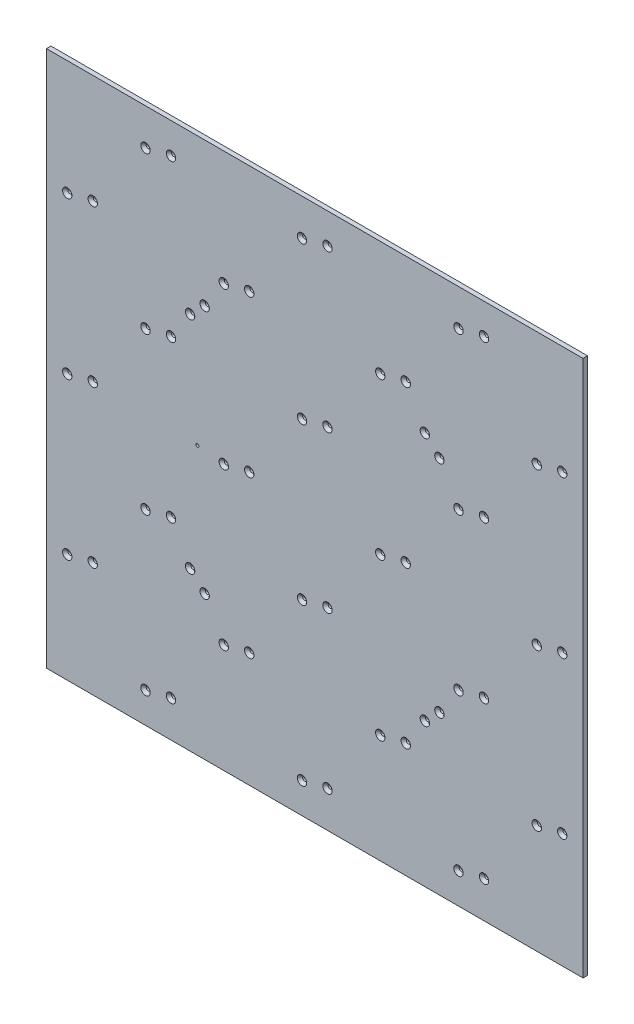
SolidWorks part; units mm, degrees
material "6063-T1"
ref_plane "Front Plane" through (0, 0, 0) normal (0, 0, 1) x (1, 0, 0)
ref_plane "Top Plane" through (0, 0, 0) normal (0, 1, 0) x (1, 0, 0)
ref_plane "Right Plane" through (0, 0, 0) normal (1, 0, 0) x (0, 0, -1)
sketch "Sketch1" plane through (0, 0, 0) normal (0, 0, 1) x (1, 0, 0)
  line L1 (600, -600) -> (-600, -600)
  line L2 (600, -600) -> (600, 600)
  line L3 (600, 600) -> (-600, 600)
  line L4 (-600, -600) -> (-600, 600)
  line L5 (600, -600) -> (-600, 600) construction
  line L6 (600, 600) -> (-600, -600) construction
  point P0 (0, 0)
  dimension "D1" = 1200
  dimension "D2" = 1200
extrude "Boss-Extrude1" add sketch "Sketch1" against normal blind 10 from offset 3
sketch "Sketch2" plane through (0, 0, -7) normal (0, 0, -1) x (-1, 0, 0)
  circle A0 centre (246.2365, -278.7635) radius 4.5
  circle A1 centre (278.7635, -246.2365) radius 4.5
  circle A2 centre (-246.2365, -278.7635) radius 4.5
  circle A3 centre (-278.7635, -246.2365) radius 4.5
  circle A4 centre (-278.7635, 246.2365) radius 4.5
  circle A5 centre (-246.2365, 278.7635) radius 4.5
  circle A6 centre (278.7635, 246.2365) radius 4.5
  circle A7 centre (246.2365, 278.7635) radius 4.5
  circle A8 centre (378.5001, -531.5724) radius 4.5
  circle A9 centre (321.5073, -518.4202) radius 4.5
  circle A10 centre (553.502, -356.5705) radius 4.5
  circle A11 centre (496.5092, -343.4183) radius 4.5
  circle A12 centre (28.4964, -531.5724) radius 4.5
  circle A13 centre (-28.4964, -518.4202) radius 4.5
  circle A14 centre (203.4983, -356.5705) radius 4.5
  circle A15 centre (146.5055, -343.4183) radius 4.5
  circle A16 centre (378.5001, -181.5687) radius 4.5
  circle A17 centre (321.5073, -168.4165) radius 4.5
  circle A18 centre (553.502, -6.5668) radius 4.5
  circle A19 centre (496.5092, 6.5854) radius 4.5
  circle A20 centre (553.502, 343.4369) radius 4.5
  circle A21 centre (496.5092, 356.5891) radius 4.5
  circle A22 centre (378.5001, 518.4388) radius 4.5
  circle A23 centre (321.5073, 531.591) radius 4.5
  circle A24 centre (378.5001, 168.4351) radius 4.5
  circle A25 centre (321.5073, 181.5872) radius 4.5
  circle A26 centre (203.4983, 343.4369) radius 4.5
  circle A27 centre (146.5055, 356.5891) radius 4.5
  circle A28 centre (203.4983, -6.5668) radius 4.5
  circle A29 centre (146.5055, 6.5854) radius 4.5
  circle A30 centre (28.4964, 168.4351) radius 4.5
  circle A31 centre (-28.4964, 181.5872) radius 4.5
  circle A32 centre (28.4964, -181.5687) radius 4.5
  circle A33 centre (-28.4964, -168.4165) radius 4.5
  circle A34 centre (-146.5055, -6.5668) radius 4.5
  circle A35 centre (-203.4983, 6.5854) radius 4.5
  circle A36 centre (-146.5055, -356.5705) radius 4.5
  circle A37 centre (-203.4983, -343.4183) radius 4.5
  circle A38 centre (-321.5073, -181.5687) radius 4.5
  circle A39 centre (-378.5001, -168.4165) radius 4.5
  circle A40 centre (-553.502, -343.4183) radius 4.5
  circle A41 centre (-496.5092, -356.5705) radius 4.5
  circle A42 centre (-378.5001, -518.4202) radius 4.5
  circle A43 centre (-321.5073, -531.5724) radius 4.5
  circle A44 centre (28.4964, 518.4388) radius 4.5
  circle A45 centre (-28.4964, 531.591) radius 4.5
  circle A46 centre (-321.5073, 518.4388) radius 4.5
  circle A47 centre (-378.5001, 531.591) radius 4.5
  circle A48 centre (-146.5055, 343.4369) radius 4.5
  circle A49 centre (-203.4983, 356.5891) radius 4.5
  circle A50 centre (-496.5092, 343.4369) radius 4.5
  circle A51 centre (-553.502, 356.5891) radius 4.5
  circle A52 centre (-321.5073, 168.4351) radius 4.5
  circle A53 centre (-378.5001, 181.5872) radius 4.5
  circle A54 centre (-496.5092, -6.5668) radius 4.5
  circle A55 centre (-553.502, 6.5854) radius 4.5
  dimension "D1" = 9
extrude "Cut-Extrude1" cut sketch "Sketch2" against normal through all
chamfer "Chamfer1" distance 6 angle 45 56 edges at (-250.7365, -278.7635, 3) (-283.2635, -246.2365, 3) (241.7365, -278.7635, 3) (274.2635, -246.2365, 3) (274.2635, 246.2365, 3) (241.7365, 278.7635, 3) (-283.2635, 246.2365, 3) (-250.7365, 278.7635, 3) (-383.0001, -531.5724, 3) (-326.0073, -518.4202, 3) (-558.002, -356.5705, 3) (-501.0092, -343.4183, 3) (-32.9964, -531.5724, 3) (23.9964, -518.4202, 3) (-207.9983, -356.5705, 3) (-151.0055, -343.4183, 3) (-383.0001, -181.5687, 3) (-326.0073, -168.4165, 3) (-558.002, -6.5668, 3) (-501.0092, 6.5854, 3) (-558.002, 343.4369, 3) (-501.0092, 356.5891, 3) (-383.0001, 518.4388, 3) (-326.0073, 531.591, 3) (-383.0001, 168.4351, 3) (-326.0073, 181.5872, 3) (-207.9983, 343.4369, 3) (-151.0055, 356.5891, 3) (-207.9983, -6.5668, 3) (-151.0055, 6.5854, 3) (-32.9964, 168.4351, 3) (23.9964, 181.5872, 3) (-32.9964, -181.5687, 3) (23.9964, -168.4165, 3) (142.0055, -6.5668, 3) (198.9983, 6.5854, 3) (142.0055, -356.5705, 3) (198.9983, -343.4183, 3) (317.0073, -181.5687, 3) (374.0001, -168.4165, 3) (549.002, -343.4183, 3) (492.0092, -356.5705, 3) (374.0001, -518.4202, 3) (317.0073, -531.5724, 3) (-32.9964, 518.4388, 3) (23.9964, 531.591, 3) (317.0073, 518.4388, 3) (374.0001, 531.591, 3) (142.0055, 343.4369, 3) (198.9983, 356.5891, 3) (492.0092, 343.4369, 3) (549.002, 356.5891, 3) (317.0073, 168.4351, 3) (374.0001, 181.5872, 3) (492.0092, -6.5668, 3) (549.002, 6.5854, 3)
sketch "Sketch3" plane through (0, 0, 3) normal (0, 0, 1) x (1, 0, 0)
  circle A0 centre (-262.5, 0) radius 3.4
  dimension "D1" = 6.8
extrude "Cut-Extrude2" cut sketch "Sketch3" against normal up to next
sketch "Sketch6" plane through (0, 0, 3) normal (0, 0, 1) x (1, 0, 0)
  line L0 (-350, 525) -> (-350, -525) construction
  line L1 (-525, 525) -> (525, 525) construction
  line L2 (-525, 525) -> (-525, -525) construction
  line L3 (-525, -525) -> (525, -525) construction
  line L4 (525, 525) -> (525, -525) construction
  line L5 (-525, 525) -> (525, -525) construction
  line L6 (-525, -525) -> (525, 525) construction
  line L7 (-175, 525) -> (-175, -525) construction
  line L8 (0, 525) -> (0, -525) construction
  line L9 (175, 525) -> (175, -525) construction
  line L10 (350, 525) -> (350, -525) construction
  line L11 (-525, 350) -> (525, 350) construction
  line L12 (-525, 175) -> (525, 175) construction
  line L13 (-525, 0) -> (525, 0) construction
  line L14 (-525, -175) -> (525, -175) construction
  line L15 (-525, -350) -> (525, -350) construction
  line L16 (175, 350) -> (350, 175) construction
  line L17 (535.6066, 45.9619) -> (570.9619, 10.6066) construction
  line L18 (535.6066, 45.9619) -> (479.0381, -10.6066) construction
  line L19 (479.0381, -10.6066) -> (514.3934, -45.9619) construction
  line L20 (570.9619, 10.6066) -> (514.3934, -45.9619) construction
  line L21 (535.6066, 45.9619) -> (514.3934, -45.9619) construction
  line L22 (479.0381, -10.6066) -> (570.9619, 10.6066) construction
  line L23 (350, -175) -> (175, -350) construction
  line L24 (-175, -350) -> (-350, -175) construction
  line L25 (-350, 175) -> (-175, 350) construction
  circle A1 centre (496.5092, -6.5668) radius 4.5
  circle A2 centre (496.5092, -6.5668) radius 4.5
  circle A3 centre (553.502, 6.5854) radius 4.5
  circle A4 centre (553.502, 6.5854) radius 4.5
  point P0 (0, 0)
  point P47 (0, 0)
  dimension "D1" = 1050
  dimension "D3" = 175
  dimension "D5" = 175
  dimension "D6" = 80
  dimension "D7" = 50
  dimension "D8" = 0
  dimension "D9" = 0
  dimension "D2" = 6
  dimension "D4" = 6
  dimension "D10" = 4
